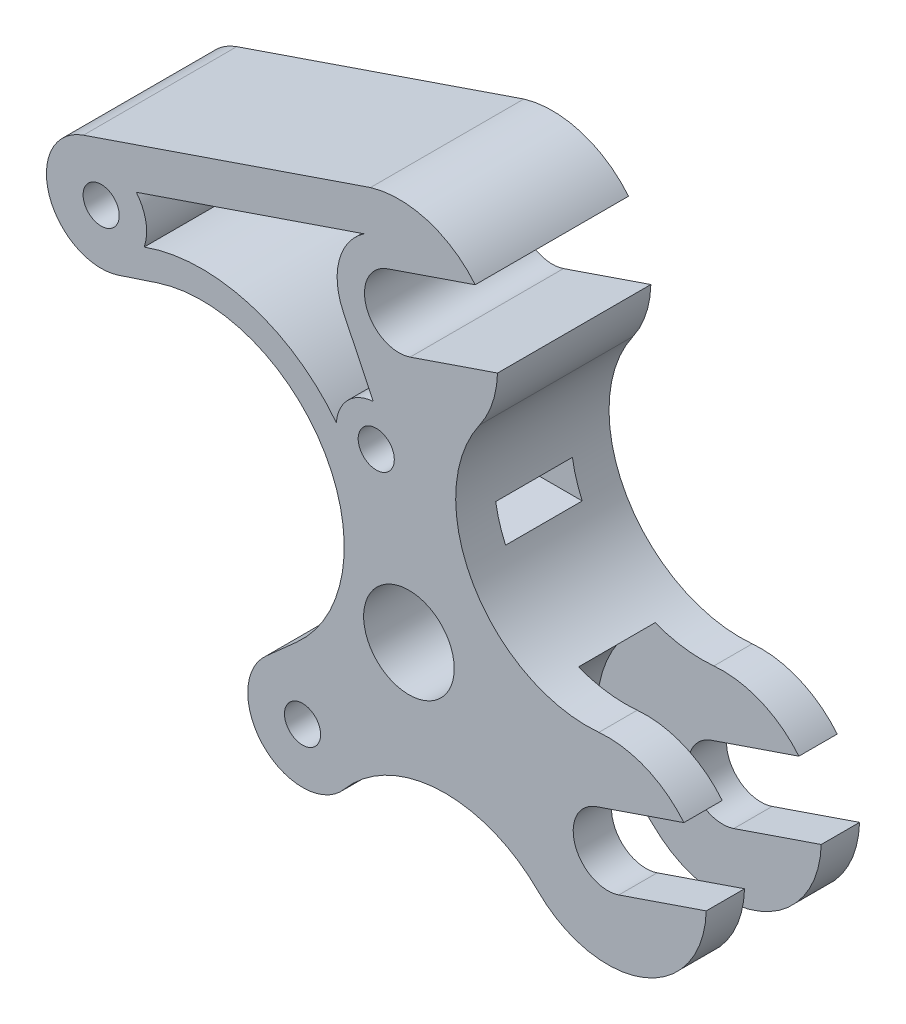
SolidWorks part; units mm, degrees
ref_plane "Front Plane" through (0, 0, 0) normal (0, 0, 1) x (1, 0, 0)
ref_plane "Top Plane" through (0, 0, 0) normal (0, 1, 0) x (1, 0, 0)
ref_plane "Right Plane" through (0, 0, 0) normal (1, 0, 0) x (0, 0, -1)
ref_plane "Plane1" through (0, 0, 7) normal (0, 0, 1) x (1, 0, 0)
sketch "Sketch1" plane through (0, 0, 0) normal (0, 0, 1) x (1, 0, 0)
  line L0 (18, 21) -> (37.0525, -11.9999) construction
  line L1 (15.9217, 9.1924) -> (-9.1924, 15.9217) construction
  line L2 (-9.1924, 15.9217) -> (-15.9217, -9.1924) construction
  line L3 (-15.9217, -9.1924) -> (9.1924, -15.9217) construction
  line L4 (9.1924, -15.9217) -> (15.9217, 9.1924) construction
  line L5 (0, 0) -> (50.7667, 0) construction
  line L6 (0, 0) -> (-9.1924, 15.9217) construction
  line L7 (-4.0727, 12.3456) -> (-7.626, 11.1734)
  line L8 (8.6552, -9.6998) -> (5.8634, -12.191)
  line L9 (0, 0) -> (9.1924, -15.9217) construction
  line L10 (15.3981, 29.6157) -> (-10.8103, 20.6527)
  line L11 (16.9807, 23.9805) -> (24.9578, 26.7086)
  line L12 (19.0193, 18.0195) -> (26.9965, 20.7476)
  line L13 (36.0332, -9.0194) -> (44.0103, -6.2913)
  line L14 (38.0718, -14.9804) -> (46.049, -12.2523)
  arc A0 (8.6552, -9.6998) -> (-4.0727, 12.3456) centre (0, 0) ccw
  arc A1 (16.9807, 23.9805) -> (19.0193, 18.0195) centre (18, 21) ccw
  circle A2 centre (-9.1924, 15.9217) radius 1.65
  circle A3 centre (15.9217, 9.1924) radius 1.65
  circle A4 centre (9.1924, -15.9217) radius 1.65
  arc A5 (25.3607, 15.8211) -> (26.9965, 20.7476) centre (18, 21) ccw
  arc A6 (36.0332, -9.0194) -> (38.0718, -14.9804) centre (37.0525, -11.9999) ccw
  arc A7 (-10.8103, 20.6527) -> (-7.626, 11.1734) centre (-9.1924, 15.9217) ccw
  arc A8 (44.0103, -6.2913) -> (36.2478, -3.0359) centre (37.0525, -11.9999) ccw
  arc A9 (30.6913, -18.3666) -> (46.049, -12.2523) centre (37.0525, -11.9999) ccw
  arc A10 (5.8634, -12.191) -> (13.021, -19.1375) centre (9.1924, -15.9217) ccw
  arc A11 (30.6913, -18.3666) -> (13.021, -19.1375) centre (22.2097, -26.8556) ccw
  arc A12 (25.3607, 15.8211) -> (36.2478, -3.0359) centre (35.1749, 8.916) ccw
  arc A13 (24.9578, 26.7086) -> (15.3981, 29.6157) centre (18, 21) ccw
  dimension "D1" = 26
  dimension "D2" = 3.3
  dimension "D3" = 6.3
  dimension "D9" = 5
  dimension "D10" = 9
  dimension "D11" = 12
  dimension "D12" = 12
  dimension "D4" = 21
  dimension "D5" = 38.105
  dimension "D6" = 60
  dimension "D7" = 18
  dimension "D8" = 15
extrude "Boss-Extrude1" add sketch "Sketch1" along normal blind 14
sketch "Sketch3" plane through (0, 0, 7) normal (0, 0, 1) x (1, 0, 0)
  line L0 (0, 7) -> (37.0525, 7)
  line L1 (-2.9117, -6.3657) -> (32.2689, -22.4578)
  line L2 (5.7446, 4) -> (37.0525, 4)
  line L3 (3.5601, -6.0271) -> (26.4728, -16.5076)
  line L4 (37.0525, 4) -> (37.0525, 7)
  line L5 (0, 4) -> (23.3288, 4) construction
  line L6 (-1.6639, -3.6375) -> (33.5168, -19.7296) construction
  line L7 (0, 7) -> (23.3288, 7) construction
  circle A0 centre (37.0525, -11.9999) radius 9.5 construction
  arc A1 (32.2689, -22.4578) -> (26.4728, -16.5076) centre (37.0525, -11.9999) ccw
  arc A2 (36.0332, -9.0194) -> (38.0718, -14.9804) centre (37.0525, -11.9999) ccw construction
  circle A3 centre (0, 0) radius 5 construction
  arc A4 (0, 7) -> (-2.9117, -6.3657) centre (0, 0) ccw
  arc A6 (3.5601, -6.0271) -> (5.7446, 4) centre (0, 0) ccw
  dimension "D1" = 19
  dimension "D2" = 2
  dimension "D3" = 10
  dimension "D4" = 2
  dimension "D5" = 3
  dimension "D6" = 3
extrude "Cut-Extrude1" cut sketch "Sketch3" against normal blind 3.5 and the other way blind 3.5
sketch "Sketch4" plane through (0, 0, 14) normal (0, 0, 1) x (1, 0, 0)
  line L0 (15.6386, 12.8314) -> (12.9012, 18.566)
  line L1 (15.3981, 29.6157) -> (-10.8103, 20.6527) construction
  line L5 (14.8177, 25.6686) -> (-5.9844, 18.5544)
  circle A0 centre (18.906, -4.6018) radius 4.1348
  arc A1 (12.2812, 9.4563) -> (-5.2659, 14.5781) centre (0, 0) ccw
  arc A2 (15.6386, 12.8314) -> (12.2812, 9.4563) centre (15.9217, 9.1924) ccw
  arc A3 (14.8177, 25.6686) -> (12.9012, 18.566) centre (18, 21) ccw
  arc A4 (-5.2659, 14.5781) -> (-5.9844, 18.5544) centre (-9.1924, 15.9217) ccw
  arc A5 (16.9807, 23.9805) -> (19.0193, 18.0195) centre (18, 21) ccw construction
  arc A6 (8.6552, -9.6998) -> (-4.0727, 12.3456) centre (0, 0) ccw construction
  circle A7 centre (15.9217, 9.1924) radius 1.65 construction
  circle A8 centre (-9.1924, 15.9217) radius 1.65 construction
  dimension "D1" = 2.5
  dimension "D2" = 2.5
  dimension "D3" = 2
  dimension "D4" = 2.5
extrude "Cut-Extrude2" cut sketch "Sketch4" against normal through all
